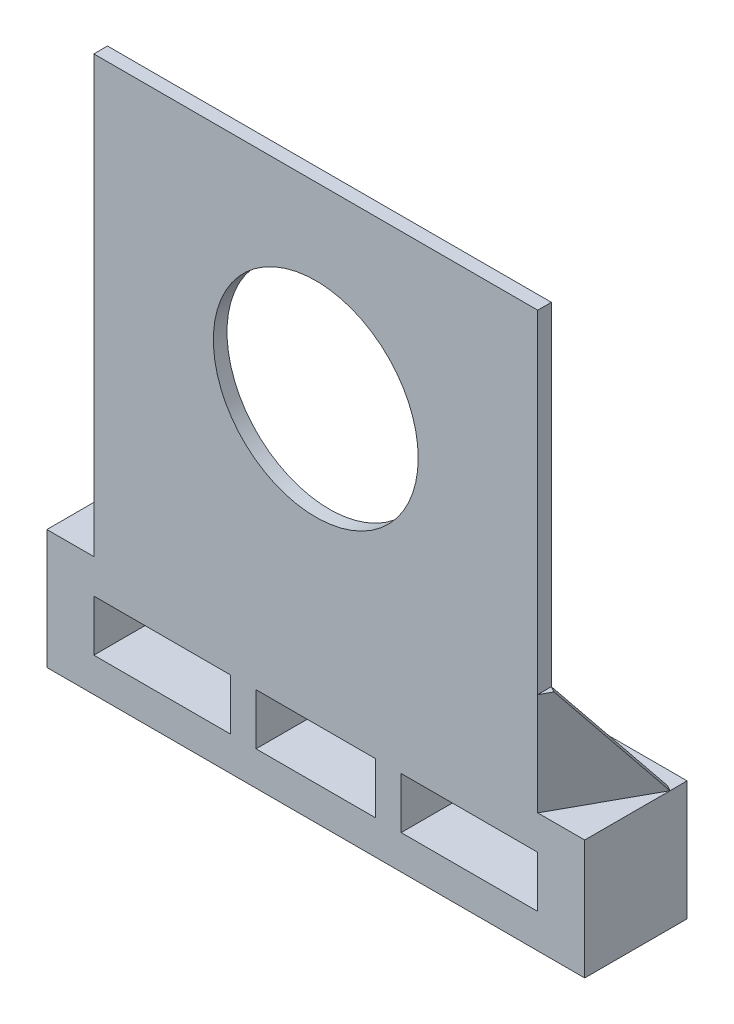
SolidWorks part; units mm, degrees
ref_plane "Front Plane" through (0, 0, 0) normal (0, 0, 1) x (1, 0, 0)
ref_plane "Top Plane" through (0, 0, 0) normal (0, 1, 0) x (1, 0, 0)
ref_plane "Right Plane" through (0, 0, 0) normal (1, 0, 0) x (0, 0, -1)
sketch "Sketch1" plane through (0, 0, 0) normal (0, 0, 1) x (1, 0, 0)
  line L21 (260, 0) -> (0, 0)
  line L27 (260, 0) -> (260, 255)
  line L28 (260, 255) -> (0, 255)
  line L29 (0, 255) -> (0, 0)
  circle A1 centre (130, 145) radius 60
  dimension "D3" = 130
  dimension "D4" = 110
  dimension "D5" = 120
  dimension "D1" = 260
  dimension "D2" = 255
extrude "Boss-Extrude1" add sketch "Sketch1" along normal blind 8
sketch "Sketch2" plane through (0, 0, 8) normal (0, 0, 1) x (1, 0, 0)
  line L0 (0, 255) -> (0, 0) construction
  line L1 (260, 255) -> (0, 255) construction
  line L2 (0, 0) -> (260, 0) construction
  line L3 (130, 0) -> (130, -20) construction
  line L4 (0, -50) -> (80, -50)
  line L5 (260, -35) -> (287.5, -35) construction
  line L8 (-27.5, 0) -> (-27.5, -70)
  line L9 (287.5, 0) -> (-27.5, 0)
  line L10 (287.5, -70) -> (287.5, 0)
  line L11 (-27.5, -70) -> (287.5, -70)
  line L15 (180, -50) -> (180, -20)
  line L16 (260, -50) -> (260, -20)
  line L17 (165, -20) -> (165, -50)
  line L18 (95, -50) -> (95, -20)
  line L19 (80, -20) -> (80, -50)
  line L20 (0, -20) -> (0, -50)
  line L21 (0, -20) -> (80, -20)
  line L22 (95, -50) -> (165, -50)
  line L23 (95, -20) -> (165, -20)
  line L24 (180, -20) -> (260, -20)
  line L25 (180, -50) -> (260, -50)
  dimension "D1" = 27.5
  dimension "D2" = 315
  dimension "D3" = 325
  dimension "D4" = 70
  dimension "D5" = 30
  dimension "D6" = 80
  dimension "D7" = 15
  dimension "D8" = 70
  dimension "D9" = 15
  dimension "D10" = 80
extrude "Boss-Extrude2" add sketch "Sketch2" against normal blind 60
sketch "Sketch3" plane through (0, 0, 0) normal (0, 1, 0) x (1, 0, 0)
  line L0 (260, -8) -> (287.5, 42)
  line L1 (287.5, 52) -> (287.5, -8) construction
  line L2 (287.5, 42) -> (284.1219, 43.858)
  line L4 (284.1219, 43.858) -> (260, 0)
  line L5 (260, -8) -> (260, 0)
  line L6 (0, -8) -> (-27.5, 42)
  line L8 (-27.5, 42) -> (-24.1219, 43.858)
  line L9 (-24.1219, 43.858) -> (0, 0)
  line L10 (0, 0) -> (0, -8)
  line L11 (-27.5, 52) -> (-27.5, -8) construction
  line L12 (0, -8) -> (-27.5, -8) construction
  dimension "D1" = 50
  dimension "D2" = 50
extrude "Boss-Extrude3" add sketch "Sketch3" along normal blind 60
sketch "Sketch4" plane through (202.9942, 0, 111.6468) normal (0.8762, 0, 0.4819) x (0.4819, 0, -0.8762)
  line L0 (175.3527, 0) -> (125.2989, 60)
  line L1 (118.2891, 60) -> (175.3527, 60) construction
  line L2 (125.2989, 60) -> (125.2989, 255) construction
  line L3 (125.2989, 60) -> (175.3527, 60)
  line L4 (175.3527, 60) -> (175.3527, 0)
extrude "Cut-Extrude1" cut sketch "Sketch4" against normal up to next
sketch "Sketch5" plane through (-3.3781, 0, 1.858) normal (-0.8762, 0, 0.4819) x (0.4819, 0, 0.8762)
  line L0 (-50.0538, 0) -> (0, 60)
  line L1 (-50.0538, 60) -> (7.0097, 60) construction
  line L2 (0, 255) -> (0, 60) construction
  line L3 (-50.0538, 0) -> (-50.0538, 60)
  line L4 (-50.0538, 60) -> (0, 60)
extrude "Cut-Extrude2" cut sketch "Sketch5" against normal up to next
